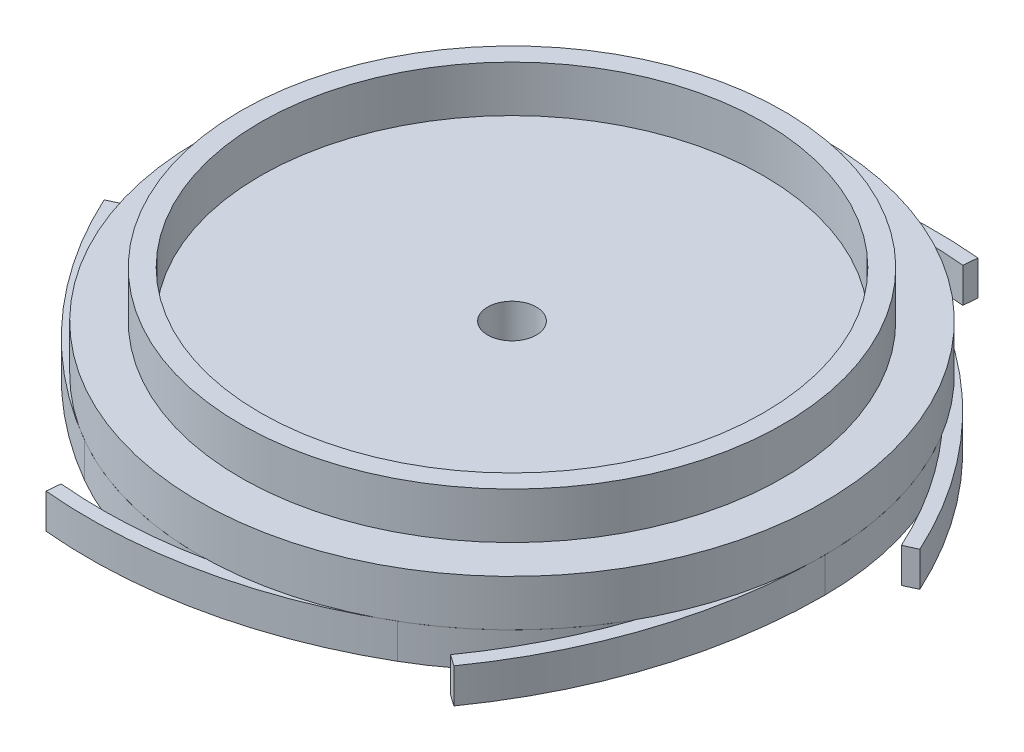
SolidWorks part; units mm, degrees
material "ABS"
ref_plane "Front" through (0, 0, 0) normal (0, 0, 1) x (1, 0, 0)
ref_plane "Top" through (0, 0, 0) normal (0, 1, 0) x (1, 0, 0)
ref_plane "Right" through (0, 0, 0) normal (1, 0, 0) x (0, 0, -1)
sketch "Sketch1" plane through (0, 0, 0) normal (0, 0, 1) x (1, 0, 0)
  line L0 (0, 0) -> (-23.425, 0) construction
  line L1 (-23.425, 0) -> (-23.425, -4)
  line L4 (-27, -8) -> (0, -8)
  line L5 (0, -8) -> (0, 0) construction
  line L6 (0, 0) -> (0, -8) construction
  line L8 (-27, -8) -> (-27, -4)
  line L9 (-27, -4) -> (-23.425, -4)
  line L10 (0, -8) -> (0, -19.7735) construction
  line L11 (-21.7215, 0) -> (-21.7215, -4)
  line L12 (-21.7215, -4) -> (0, -4)
  line L13 (-21.7215, 0) -> (-23.425, 0)
  line L14 (0, -8) -> (0, -4)
  dimension "D1" = 54
  dimension "D2" = 8
  dimension "D3" = 4
  dimension "D6" = 23.425
revolve "Revolve1" add sketch "Sketch1" angle 360 about L10
sketch "Sketch18" plane through (0, -8, 0) normal (0, -1, 0) x (1, 0, 0)
  line L0 (-15, 0) -> (19.2667, 24.2857) construction
  line L1 (18.2876, 23.5918) -> (19.2667, 24.2857)
  line L2 (13.5, 23.3827) -> (0, 0) construction
  line L3 (0, 0) -> (27, 0) construction
  line L4 (29.5749, -4.0416) -> (30.6654, -4.5426)
  line L5 (11.2873, -27.6335) -> (11.3987, -28.8283)
  line L6 (-18.2876, -23.5918) -> (-19.2667, -24.2857)
  line L7 (-29.5749, 4.0416) -> (-30.6654, 4.5426)
  line L8 (-11.2873, 27.6335) -> (-11.3987, 28.8283)
  circle A0 centre (0, 0) radius 27 construction
  arc A2 (23.688, 12.9568) -> (18.2876, 23.5918) centre (-15, 0) ccw
  arc A3 (27, 0) -> (19.2667, 24.2857) centre (-15, 0) ccw
  arc A4 (23.688, 12.9568) -> (13.5, 23.3827) centre (0, 0) ccw
  arc A5 (23.0649, -14.036) -> (27, 0) centre (0, 0) ccw
  arc A6 (23.0649, -14.036) -> (29.5749, -4.0416) centre (-7.5, 12.9904) ccw
  arc A7 (13.5, -23.3827) -> (30.6654, -4.5426) centre (-7.5, 12.9904) ccw
  arc A8 (-0.6231, -26.9928) -> (13.5, -23.3827) centre (0, 0) ccw
  arc A9 (-0.6231, -26.9928) -> (11.2873, -27.6335) centre (7.5, 12.9904) ccw
  arc A10 (-13.5, -23.3827) -> (11.3987, -28.8283) centre (7.5, 12.9904) ccw
  arc A11 (-23.688, -12.9568) -> (-13.5, -23.3827) centre (0, 0) ccw
  arc A12 (-23.688, -12.9568) -> (-18.2876, -23.5918) centre (15, 0) ccw
  arc A13 (-27, 0) -> (-19.2667, -24.2857) centre (15, 0) ccw
  arc A14 (-23.0649, 14.036) -> (-27, 0) centre (0, 0) ccw
  arc A15 (-23.0649, 14.036) -> (-29.5749, 4.0416) centre (7.5, -12.9904) ccw
  arc A16 (-13.5, 23.3827) -> (-30.6654, 4.5426) centre (7.5, -12.9904) ccw
  arc A17 (0.6231, 26.9928) -> (-13.5, 23.3827) centre (0, 0) ccw
  arc A18 (0.6231, 26.9928) -> (-11.2873, 27.6335) centre (-7.5, -12.9904) ccw
  arc A19 (13.5, 23.3827) -> (-11.3987, 28.8283) centre (-7.5, -12.9904) ccw
  dimension "D1" = 1.2
  dimension "D2" = 15
  dimension "D3" = 60
  dimension "D4" = 31
  dimension "D5" = 27
  dimension "D6" = 1.2
extrude "Boss-Extrude1" add sketch "Sketch18" along normal blind 3
sketch "Sketch19" plane through (0, -11, 0) normal (0, -1, 0) x (1, 0, 0)
  line L1 (0, -4.1569) -> (3.6, -2.0785)
  line L2 (3.6, -2.0785) -> (3.6, 2.0785)
  line L3 (3.6, 2.0785) -> (0, 4.1569)
  line L4 (0, 4.1569) -> (-3.6, 2.0785)
  line L5 (-3.6, 2.0785) -> (-3.6, -2.0785)
  line L6 (-3.6, -2.0785) -> (0, -4.1569)
  circle A0 centre (0, 0) radius 3.6 construction
  dimension "D1" = 7.2
hole_wizard "Ø4.2 (4.2) Diameter Hole1" positions "Sketch21" profile "Sketch23" hole size "Ø4.2" standard "GB" end condition through all
sketch "Sketch21" plane through (0, -4, 0) normal (0, 1, 0) x (1, 0, 0)
  point P0 (0, 0)
sketch "Sketch23" plane through (0, -4, 0) normal (1, 0, 0) x (0, 0, 1)
  line L0 (0, 0) -> (0, 7)
  line L1 (0, 7) -> (2.1, 7)
  line L2 (2.1, 7) -> (2.1, 0)
  line L5 (2.1, 0) -> (0, 0)
  line L11 (0, -6.35) -> (0, 107.95) construction
  dimension "Thru Hole Dia." = 4.2
  dimension "Thru Hole Depth" = 7
extrude "Cut-Extrude1" cut sketch "Sketch19" against normal blind 4
